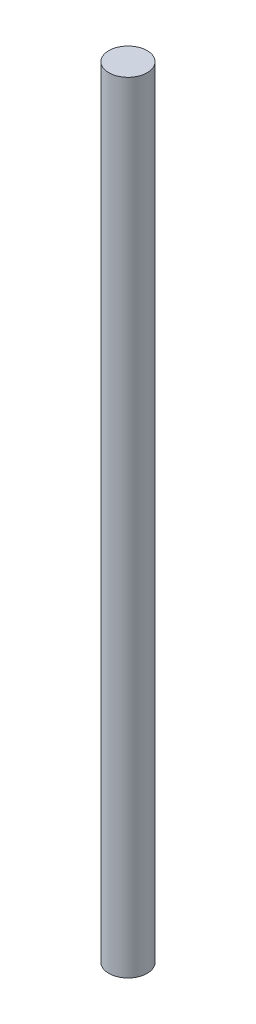
SolidWorks part; units mm, degrees
ref_plane "Front" through (0, 0, 0) normal (0, 0, 1) x (1, 0, 0)
ref_plane "Top" through (0, 0, 0) normal (0, 1, 0) x (1, 0, 0)
ref_plane "Right" through (0, 0, 0) normal (1, 0, 0) x (0, 0, -1)
sketch "Sketch1" plane through (0, 0, 0) normal (0, 1, 0) x (1, 0, 0)
  circle A0 centre (0, 0) radius 1.5
  dimension "D1" = 3
extrude "Boss-Extrude1" add sketch "Sketch1" along normal blind 61
